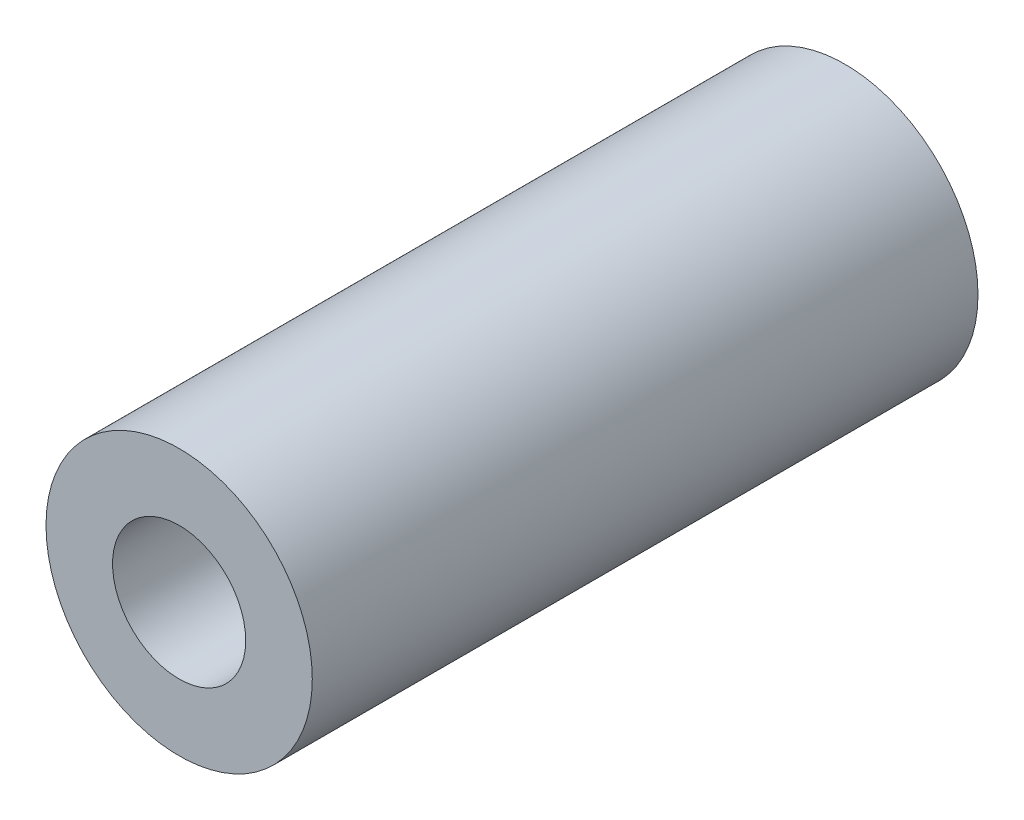
SolidWorks part; units mm, degrees
ref_plane "Front Plane" through (0, 0, 0) normal (0, 0, 1) x (1, 0, 0)
ref_plane "Top Plane" through (0, 0, 0) normal (0, 1, 0) x (1, 0, 0)
ref_plane "Right Plane" through (0, 0, 0) normal (1, 0, 0) x (0, 0, -1)
sketch "Sketch1" plane through (0, 0, 0) normal (0, 0, 1) x (1, 0, 0)
  circle A0 centre (0, 0) radius 2
  circle A1 centre (0, 0) radius 1
  point P4 (3.1434, -4.1318)
  dimension "D1" = 4
  dimension "D2" = 2
extrude "Boss-Extrude1" add sketch "Sketch1" along normal blind 10
sketch "Sketch2" plane through (0, 0, 0) normal (1, 0, 0) x (0, 0, -1)
  line L0 (-4, 0) -> (0, 0) construction
  line L1 (0, -2) -> (0, 2) construction
  circle A0 centre (-4, 0) radius 1.2891
  dimension "D1" = 2.5781
  dimension "D2" = 4
extrude "hole for 5-40 set screw" cut sketch "Sketch2" against normal through all
